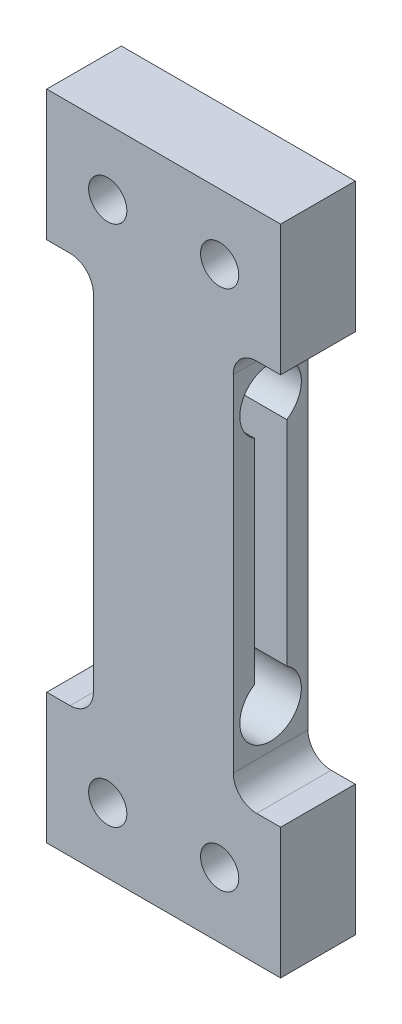
SolidWorks part; units mm, degrees
ref_plane "Front Plane" through (0, 0, 0) normal (0, 0, 1) x (1, 0, 0)
ref_plane "Top Plane" through (0, 0, 0) normal (0, 1, 0) x (1, 0, 0)
ref_plane "Right Plane" through (0, 0, 0) normal (1, 0, 0) x (0, 0, -1)
ref_plane "Plane1" through (0, 0, 4) normal (0, 0, 1) x (1, 0, 0)
sketch "Sketch1" plane through (0, 0, 4) normal (0, 0, 1) x (1, 0, 0)
  line L0 (-10, 35) -> (-10, 0)
  line L1 (-10, 0) -> (2.5384, 0)
  line L2 (2.5384, 0) -> (2.5384, 35)
  line L3 (2.5384, 35) -> (-10, 35)
extrude "Boss-Extrude1" add sketch "Sketch1" against normal blind 4
sketch "Sketch2" plane through (0, 0, 0) normal (0, 0, -1) x (-1, 0, 0)
  line L0 (10, 28) -> (7.5, 28)
  line L1 (7.5, 28) -> (7.5, 7)
  line L2 (7.5, 7) -> (10, 7)
  line L3 (10, 7) -> (10, 28)
extrude "Cut-Extrude1" cut sketch "Sketch2" against normal through all
sketch "Sketch3" plane through (0, 0, 0) normal (0, 0, -1) x (-1, 0, 0)
  line L0 (-2.5384, 7) -> (0, 7)
  line L1 (0, 7) -> (0, 28)
  line L2 (0, 28) -> (-2.5384, 28)
  line L3 (-2.5384, 28) -> (-2.5384, 7)
extrude "Cut-Extrude2" cut sketch "Sketch3" against normal through all
sketch "Sketch4" plane through (-7.5, 0, 0) normal (-1, 0, 0) x (0, 0, 1)
  line L0 (2.8559, 11.7856) -> (2.8559, 23.2144)
  line L1 (1.1318, 23.2219) -> (1.1318, 11.7781)
  arc A0 (1.1318, 11.7781) -> (2.8559, 11.7856) centre (2, 10.375) cw
  arc A1 (2.8559, 23.2144) -> (1.1318, 23.2219) centre (2, 24.625) cw
extrude "Cut-Extrude3" cut sketch "Sketch4" against normal through all
ref_plane "Plane2" through (0, 0, 2) normal (0, 0, -1) x (-1, 0, 0)
sketch "Sketch5" plane through (0, 0, 2) normal (0, 0, -1) x (-1, 0, 0)
  line L0 (0, 26.275) -> (0, 24.625)
  line L1 (0, 24.625) -> (7.5, 24.625)
  line L2 (7.5, 24.625) -> (7.5, 26.275)
  line L3 (7.5, 26.275) -> (0, 26.275)
  line L4 (0, 24.625) -> (7.5, 24.625) construction
revolve "Cut-Revolve1" cut sketch "Sketch5" angle 360 about L4
sketch "Sketch6" plane through (0, 0, 2) normal (0, 0, -1) x (-1, 0, 0)
  line L0 (0, 12.025) -> (0, 10.375)
  line L1 (0, 10.375) -> (7.5, 10.375)
  line L2 (7.5, 10.375) -> (7.5, 12.025)
  line L3 (7.5, 12.025) -> (0, 12.025)
  line L4 (0, 10.375) -> (7.5, 10.375) construction
revolve "Cut-Revolve2" cut sketch "Sketch6" angle 360 about L4
hole_wizard "M2.5x0.45 Tapped Hole1" positions "Sketch8" profile "Sketch7" tap size "M2.5x0.45" standard "Ansi Metric" end condition through all
sketch "Sketch8" plane through (0, 0, 4) normal (0, 0, 1) x (1, 0, 0)
  point P0 (-0.7308, 3.5)
  point P1 (-6.7308, 3.5)
  point P2 (-0.7308, 31.5)
  point P3 (-6.7308, 31.5)
sketch "Sketch7" plane through (-0.7308, 3.5, 4) normal (1, 0, 0) x (0, -1, 0)
  line L0 (0, 0) -> (0, 4)
  line L1 (0, 4) -> (1.025, 4)
  line L2 (1.025, 4) -> (1.025, 0)
  line L5 (1.025, 0) -> (0, 0)
  line L11 (0, -6.35) -> (0, 107.95) construction
  dimension "Thread Major Dia." = 2.05
  dimension "Thru Tap Drill Depth" = 4
fillet "Fillet1" radius 1.25 4 edges at (-7.5, 28, 2) (-7.5, 7, 2) (0, 28, 2) (0, 7, 2)
